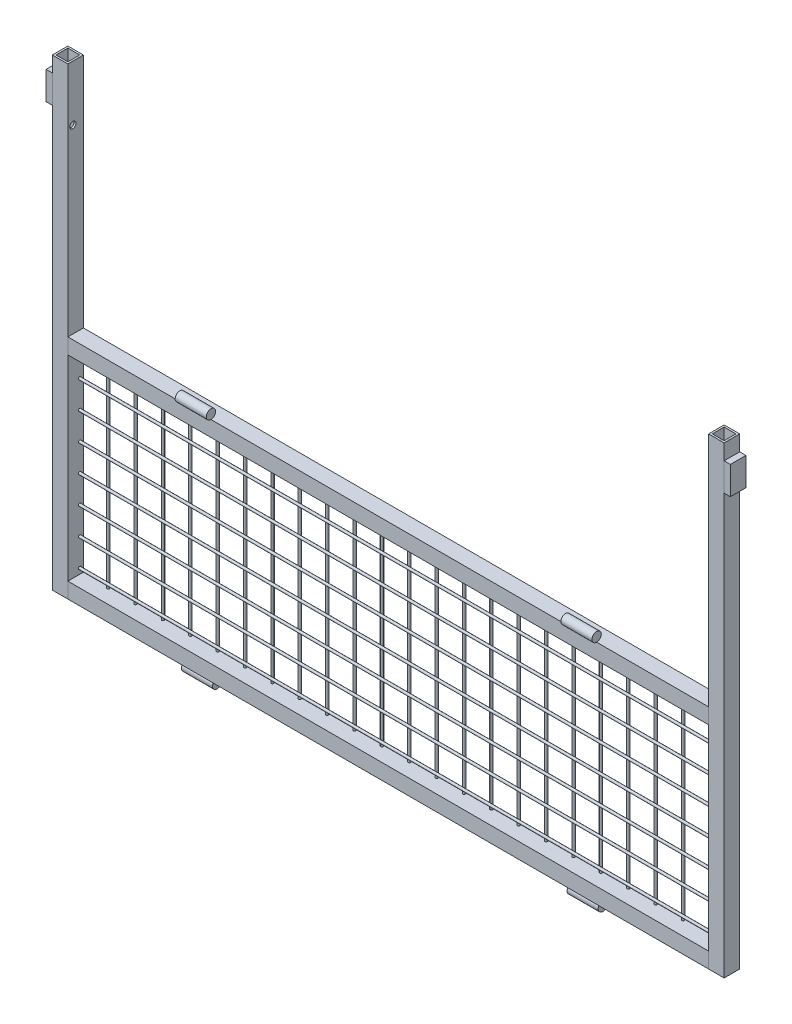
SolidWorks part; units mm, degrees
ref_plane "Piano frontale" through (0, 0, 0) normal (0, 0, 1) x (1, 0, 0)
ref_plane "Piano superiore" through (0, 0, 0) normal (0, 1, 0) x (1, 0, 0)
ref_plane "Piano destro" through (0, 0, 0) normal (1, 0, 0) x (0, 0, -1)
sketch "Schizzo1" plane through (0, 0, 0) normal (0, 1, 0) x (1, 0, 0)
  line L0 (-537, 9.5) -> (-518, 9.5)
  line L1 (-540, -12.5) -> (-515, -12.5)
  line L2 (-540, -12.5) -> (-540, 12.5)
  line L3 (-540, 12.5) -> (-515, 12.5)
  line L4 (-515, -12.5) -> (-515, 12.5)
  line L5 (-518, -9.5) -> (-518, 9.5)
  line L6 (-537, -9.5) -> (-518, -9.5)
  line L7 (-537, -9.5) -> (-537, 9.5)
  line L8 (0, 0) -> (0, 211.96) construction
  line L9 (537, -9.5) -> (537, 9.5)
  line L10 (537, -9.5) -> (518, -9.5)
  line L11 (518, -9.5) -> (518, 9.5)
  line L12 (515, -12.5) -> (515, 12.5)
  line L13 (540, 12.5) -> (515, 12.5)
  line L14 (540, -12.5) -> (540, 12.5)
  line L15 (540, -12.5) -> (515, -12.5)
  line L16 (537, 9.5) -> (518, 9.5)
  point P4 (-515, 0)
  dimension "D1" = 25
  dimension "D2" = 25
  dimension "D3" = 540
  dimension "D4" = 3
extrude "Estrusione-Estrusione1" add sketch "Schizzo1" along normal blind 745
sketch "Schizzo2" plane through (-515, 0, 0) normal (1, 0, 0) x (0, 0, -1)
  line L0 (12.5, 745) -> (12.5, 0) construction
  line L1 (-12.5, 0) -> (12.5, 0)
  line L2 (-12.5, 0) -> (-12.5, 25)
  line L3 (-12.5, 25) -> (12.5, 25)
  line L4 (12.5, 0) -> (12.5, 25)
  line L5 (-9.5, 22) -> (9.5, 22)
  line L6 (9.5, 3) -> (9.5, 22)
  line L7 (-9.5, 3) -> (9.5, 3)
  line L8 (-9.5, 3) -> (-9.5, 22)
  line L9 (-12.5, 745) -> (-12.5, 0) construction
  line L11 (-12.5, 365) -> (12.5, 365)
  line L12 (-12.5, 365) -> (-12.5, 340)
  line L13 (-12.5, 340) -> (12.5, 340)
  line L14 (12.5, 365) -> (12.5, 340)
  line L15 (-9.5, 362) -> (9.5, 362)
  line L16 (9.5, 362) -> (9.5, 343)
  line L17 (-9.5, 343) -> (9.5, 343)
  line L18 (-9.5, 362) -> (-9.5, 343)
  dimension "D1" = 25
  dimension "D4" = 365
  dimension "D5" = 25
  dimension "D2" = 3
  dimension "D3" = 3
extrude "Estrusione-Estrusione2" add sketch "Schizzo2" along normal up to next (1030 mm away) separate body
ref_plane "Piano1" through (335, 0, 0) normal (1, 0, 0) x (0, 0, -1)
sketch "Schizzo4" plane through (335, 0, 0) normal (1, 0, 0) x (0, 0, -1)
  line L0 (12.5, 0) -> (12.5, -15.4835) construction
  line L1 (-12.5, 0) -> (12.5, 0) construction
  line L2 (-12.5, 745) -> (-12.5, 0) construction
  line L4 (12.5, 365) -> (-12.5, 365) construction
  circle A0 centre (-2.5, -7.5) radius 7.5
  circle A1 centre (-12.5, 372.5) radius 7.5
  dimension "D1" = 15
  dimension "D2" = 15
  dimension "D3" = 15
extrude "Estrusione-Estrusione3" add sketch "Schizzo4" against normal blind 50 separate body
mirror "Specchia1" about plane through (0, 0, 0) normal (1, 0, 0) of bodies 105 126
sketch "Schizzo5" plane through (540, 0, 0) normal (1, 0, 0) x (0, 0, -1)
  line L0 (-12.5, 745) -> (-12.5, 0) construction
  line L1 (-12.5, 720) -> (12.5, 720)
  line L2 (-12.5, 720) -> (-12.5, 675)
  line L3 (-12.5, 675) -> (12.5, 675)
  line L4 (12.5, 720) -> (12.5, 675)
  line L5 (12.5, 745) -> (12.5, 0) construction
  line L6 (-12.5, 745) -> (12.5, 745) construction
  dimension "D1" = 25
  dimension "D2" = 45
extrude "Estrusione-Estrusione4" add sketch "Schizzo5" along normal blind 10 separate body
mirror "Specchia2" about plane through (0, 0, 0) normal (1, 0, 0) of bodies 107
sketch "Schizzo6" plane through (0, 25, 0) normal (0, 1, 0) x (1, 0, 0)
  line L0 (-515, 12.5) -> (-515, -12.5) construction
  line L1 (515, 12.5) -> (-515, 12.5) construction
  line L2 (-473, 10.5) -> (-429, 10.5) construction
  circle A0 centre (-473, 10.5) radius 2
  circle A1 centre (-429, 10.5) radius 2
  circle A2 centre (-385, 10.5) radius 2
  circle A3 centre (-341, 10.5) radius 2
  circle A4 centre (-297, 10.5) radius 2
  circle A5 centre (-253, 10.5) radius 2
  circle A6 centre (-209, 10.5) radius 2
  circle A7 centre (-165, 10.5) radius 2
  circle A8 centre (-121, 10.5) radius 2
  circle A9 centre (-77, 10.5) radius 2
  circle A10 centre (-33, 10.5) radius 2
  circle A11 centre (11, 10.5) radius 2
  circle A12 centre (55, 10.5) radius 2
  circle A13 centre (99, 10.5) radius 2
  circle A14 centre (143, 10.5) radius 2
  circle A15 centre (187, 10.5) radius 2
  circle A16 centre (231, 10.5) radius 2
  circle A17 centre (275, 10.5) radius 2
  circle A18 centre (319, 10.5) radius 2
  circle A19 centre (363, 10.5) radius 2
  circle A20 centre (407, 10.5) radius 2
  circle A21 centre (451, 10.5) radius 2
  circle A22 centre (495, 10.5) radius 2
  dimension "D1" = 4
  dimension "D2" = 42
  dimension "D4" = 44
  dimension "D3" = 23
extrude "Estrusione-Estrusione5" add sketch "Schizzo6" along normal up to next (315 mm away)
sketch "Schizzo7" plane through (-515, 0, 0) normal (1, 0, 0) x (0, 0, -1)
  line L0 (-12.5, 340) -> (12.5, 340) construction
  line L2 (6.5, 298) -> (6.5, 254) construction
  line L3 (8.5, 340) -> (8.5, 25) construction
  circle A0 centre (6.5, 298) radius 2
  circle A1 centre (6.5, 254) radius 2
  circle A2 centre (6.5, 210) radius 2
  circle A3 centre (6.5, 166) radius 2
  circle A4 centre (6.5, 122) radius 2
  circle A5 centre (6.5, 78) radius 2
  circle A6 centre (6.5, 34) radius 2
  dimension "D1" = 4
  dimension "D2" = 42
  dimension "D4" = 44
  dimension "D3" = 7
extrude "Estrusione-Estrusione7" add sketch "Schizzo7" along normal up to next (1030 mm away) separate body
sketch "Schizzo8" plane through (540, 0, 0) normal (1, 0, 0) x (0, 0, -1)
  line L0 (-9.5, 745) -> (-9.5, 0) construction
  line L1 (-12.5, 745) -> (12.5, 745) construction
  circle A0 centre (-4.5, 656) radius 5
  dimension "D1" = 10
  dimension "D2" = 89
extrude "Taglio-Estrusione1" cut sketch "Schizzo8" against normal up to surface (1036 mm away) from surface at -22 up to face at (-518, 372.5, 0) starting at face at (518, 372.5, 0)
